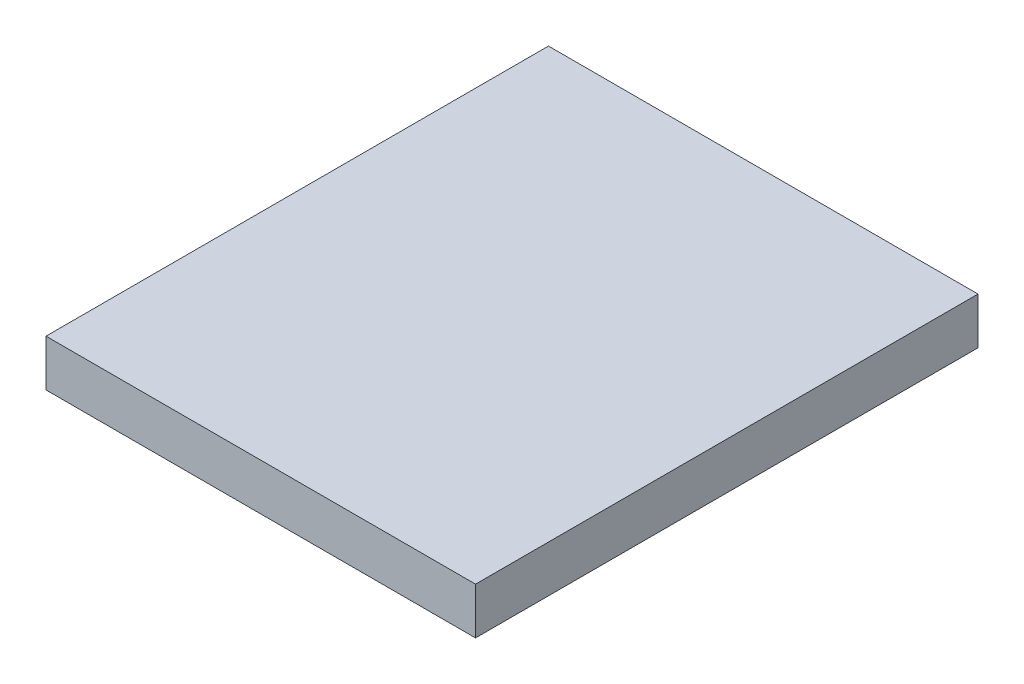
SolidWorks part; units mm, degrees
ref_plane "Front Plane" through (0, 0, 0) normal (0, 0, 1) x (1, 0, 0)
ref_plane "Top Plane" through (0, 0, 0) normal (0, 1, 0) x (1, 0, 0)
ref_plane "Right Plane" through (0, 0, 0) normal (1, 0, 0) x (0, 0, -1)
sketch "Sketch1" plane through (0, 0, 0) normal (0, 1, 0) x (1, 0, 0)
  line L1 (-26.5, -31) -> (26.5, -31)
  line L2 (-26.5, -31) -> (-26.5, 31)
  line L3 (-26.5, 31) -> (26.5, 31)
  line L4 (26.5, -31) -> (26.5, 31)
  line L5 (-26.5, -31) -> (26.5, 31) construction
  line L6 (-26.5, 31) -> (26.5, -31) construction
  point P0 (0, 0)
  dimension "D1" = 53
  dimension "D2" = 62
extrude "Boss-Extrude1" add sketch "Sketch1" along normal blind 5.75
